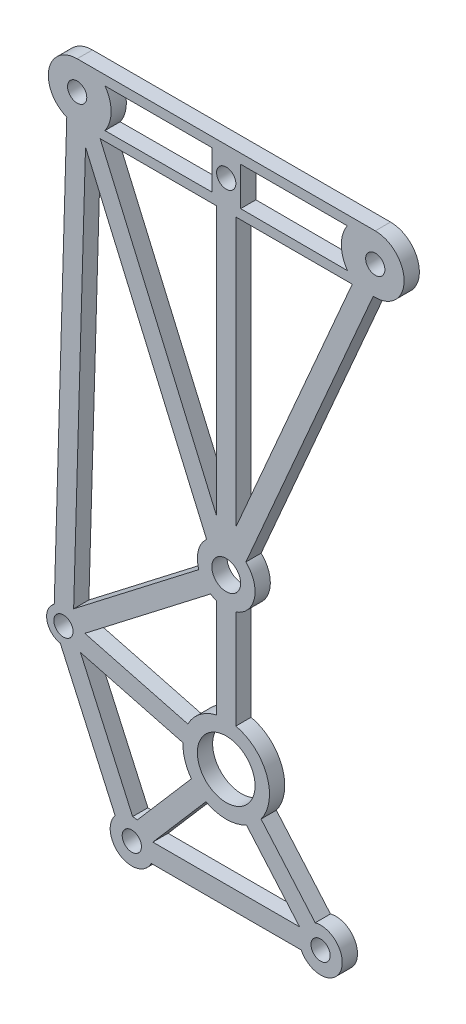
SolidWorks part; units mm, degrees
ref_plane "Front Plane" through (0, 0, 0) normal (0, 0, 1) x (1, 0, 0)
ref_plane "Top Plane" through (0, 0, 0) normal (0, 1, 0) x (1, 0, 0)
ref_plane "Right Plane" through (0, 0, 0) normal (1, 0, 0) x (0, 0, -1)
sketch "Sketch3" plane through (0, 0, 0) normal (0, 0, 1) x (1, 0, 0)
  line L0 (-11.5, 31.6412) -> (19.5, 31.6412)
  line L1 (-9.1094, 25.6412) -> (3, 25.6412)
  line L2 (5.5, 30.6412) -> (5.5, 26.6412)
  line L3 (5.5, 26.6412) -> (16.6125, 26.613)
  line L4 (2.5, 30.6412) -> (-8.5929, 30.6412)
  line L5 (2.5, 26.6412) -> (-8.6125, 26.613)
  line L6 (2.5, 30.6412) -> (2.5, 26.6412)
  line L7 (5.5, 30.6412) -> (16.5929, 30.6412)
  line L9 (3, -20.2125) -> (3, -9.9372)
  line L10 (5, 25.6412) -> (17.1094, 25.6412)
  line L11 (-10.7052, -19.7103) -> (0.0096, -22.5199)
  line L12 (1.1495, -8.044) -> (-11.8664, -18.0802)
  line L13 (2.3707, -9.6278) -> (-10.7052, -19.7103)
  line L14 (-3.7996, -36.9751) -> (11.7996, -36.9751)
  line L15 (-3.6315, -34.9751) -> (11.6315, -34.9751)
  line L20 (-13.2506, -21.8813) -> (-7.5539, -34.5471)
  line L21 (-3.6315, -34.9751) -> (1.8908, -28.5751)
  line L22 (-11.1575, -21.6593) -> (-0.4976, -24.4545)
  line L25 (19.2892, 25.6412) -> (19.5, 25.6412)
  line L26 (-11.1575, -21.6593) -> (-5.7299, -33.7267)
  line L29 (-5.2555, -33.7958) -> (0.3766, -27.2685)
  line L33 (-10.6317, 24.1246) -> (1.9574, -4.9116)
  line L34 (-10.6317, 24.1246) -> (-11.8664, -18.0802)
  line L39 (-9.1094, 25.6412) -> (3, -2.2884)
  line L41 (-12.5823, 25.8432) -> (-13.8853, -18.6966)
  line L42 (6.0426, -4.9116) -> (19.2892, 25.6412)
  line L44 (5, -2.2884) -> (5, 25.6412)
  line L47 (6.1092, -28.5751) -> (11.6315, -34.9751)
  line L50 (5, -2.2884) -> (17.1094, 25.6412)
  line L52 (3, -2.2884) -> (3, 25.6412)
  line L53 (7.6234, -27.2685) -> (13.2555, -33.7958)
  line L56 (5, -20.2125) -> (5, -9.9372)
  circle A0 centre (4, -24.6) radius 3
  circle A1 centre (-12.9277, -20.1613) radius 1
  circle A2 centre (4, -7.1088) radius 1.5
  circle A3 centre (-5.8152, -35.9751) radius 1
  circle A4 centre (13.8152, -35.9751) radius 1
  circle A5 centre (-11.5, 28.6412) radius 1
  circle A6 centre (4, 28.6412) radius 1
  circle A7 centre (19.5, 28.6412) radius 1
  arc A8 (-8.5929, 30.6412) -> (-8.6125, 26.613) centre (-11.5, 28.6412) cw
  arc A9 (16.5929, 30.6412) -> (16.6125, 26.613) centre (19.5, 28.6412) ccw
  arc A10 (-11.5, 31.6412) -> (-12.5823, 25.8432) centre (-11.5, 28.6412) ccw
  arc A11 (1.9574, -4.9116) -> (1.1495, -8.044) centre (4, -7.1088) ccw
  arc A12 (5, -9.9372) -> (6.0426, -4.9116) centre (4, -7.1088) ccw
  arc A13 (-7.5539, -34.5471) -> (-3.7996, -36.9751) centre (-5.8152, -35.9751) ccw
  arc A14 (11.7996, -36.9751) -> (13.2555, -33.7958) centre (13.8152, -35.9751) ccw
  arc A15 (1.8908, -28.5751) -> (6.1092, -28.5751) centre (4, -24.6) ccw
  arc A16 (3, -20.2125) -> (0.0096, -22.5199) centre (4, -24.6) ccw
  arc A17 (19.5, 25.6412) -> (19.5, 31.6412) centre (19.5, 28.6412) ccw
  arc A18 (7.6234, -27.2685) -> (5, -20.2125) centre (4, -24.6) ccw
  arc A19 (-0.4976, -24.4545) -> (0.3766, -27.2685) centre (4, -24.6) ccw
  arc A21 (-5.2555, -33.7958) -> (-5.7299, -33.7267) centre (-5.8152, -35.9751) ccw
  arc A22 (2.3707, -9.6278) -> (3, -9.9372) centre (4, -7.1088) ccw
  arc A23 (-13.8853, -18.6966) -> (-13.2506, -21.8813) centre (-12.9277, -20.1613) ccw
  point P33 (4, 30.8544)
extrude "Boss-Extrude1" add sketch "Sketch3" along normal blind 1.5875
